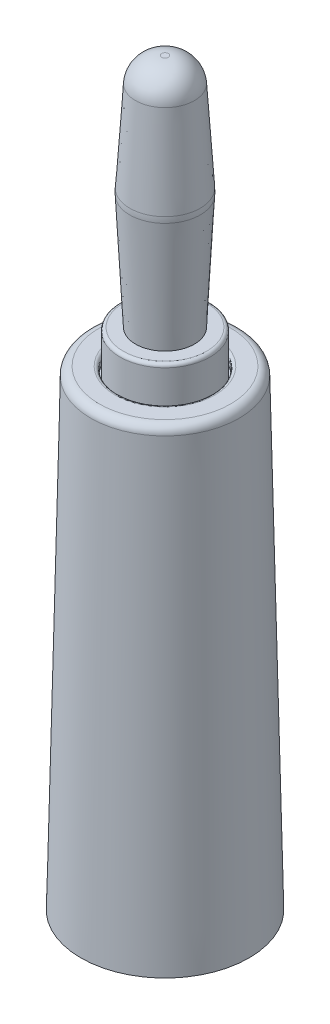
SolidWorks part; units mm, degrees
other "Plastic Cover"
other "Metal Body"
other "Tip"
material "Plain Carbon Steel"
ref_plane "Front Plane" through (0, 0, 0) normal (0, 0, 1) x (1, 0, 0)
ref_plane "Top Plane" through (0, 0, 0) normal (0, 1, 0) x (1, 0, 0)
ref_plane "Right Plane" through (0, 0, 0) normal (1, 0, 0) x (0, 0, -1)
sketch "Sketch1" plane through (0, 0, 0) normal (0, 0, 1) x (1, 0, 0)
  line L0 (0, 0) -> (0, 18)
  line L1 (0, 0) -> (3.45, 0)
  line L2 (3.45, 0) -> (3.45, 13)
  line L3 (3.45, 13) -> (2.68, 13.77)
  line L4 (2.68, 13.77) -> (2.68, 18)
  line L5 (2.68, 18) -> (0, 18)
  dimension "D1" = 2.68
  dimension "D2" = 3.45
  dimension "D3" = 13
  dimension "D4" = 18
  dimension "D5" = 135
revolve "Revolve1" add sketch "Sketch1" angle 360 about L0
sketch "Sketch2" plane through (0, 0, 0) normal (0, -1, 0) x (1, 0, 0)
  circle A0 centre (0, 0) radius 2.55
  dimension "D1" = 5.1
extrude "Cut-Extrude1" cut sketch "Sketch2" against normal blind 11
sketch "Sketch3" plane through (0, 0, 0) normal (0, 0, 1) x (1, 0, 0)
  line L0 (0, 0) -> (0, 18) construction
  line L1 (2.68, 18) -> (-2.68, 18) construction
  line L2 (0, 18) -> (0, 32)
  line L3 (0, 18) -> (1.75, 18)
  line L4 (0, 32) -> (0.2, 32)
  line L5 (1.75, 32) -> (1.75, 30.546) construction
  line L6 (0.2, 32) -> (1.75, 32) construction
  line L7 (0, 25) -> (2.1, 25) construction
  line L8 (1.75, 30.546) -> (2.0939, 25.1717)
  line L9 (2.0962, 24.8282) -> (1.75, 18)
  arc A0 (0.2, 32) -> (1.75, 30.546) centre (0.2, 30.4468) cw
  arc A1 (2.0939, 25.1717) -> (2.0962, 24.8282) centre (-0.8999, 24.9801) cw
  dimension "D6" = 3
  dimension "D1" = 14
  dimension "D2" = 1.75
  dimension "D3" = 1.75
  dimension "D4" = 7
  dimension "D5" = 0.2
  dimension "D7" = 2.1
revolve "Revolve2" add sketch "Sketch3" angle 360 about L2
shell "Shell7" thickness 0.1
sketch "Sketch4" plane through (0, 0, 0) normal (0, 0, 1) x (1, 0, 0)
  line L0 (0, 0) -> (0, 3) construction
  circle A0 centre (0, 3) radius 1.2
  dimension "D1" = 2.4
  dimension "D2" = 3
extrude "Cut-Extrude2" cut sketch "Sketch4" along normal through all
sketch "Sketch5" plane through (0, 0, 0) normal (0, 0, 1) x (1, 0, 0)
  line L0 (0, 0) -> (0, 8) construction
  circle A0 centre (0, 8) radius 1.2
  dimension "D1" = 2.4
  dimension "D2" = 8
extrude "Cut-Extrude3" cut sketch "Sketch5" against normal through all
fillet "Fillet1" radius 0.2 3 edges at (0, 18, -2.68) (0, 13.77, -2.68) (0, 13, -3.45)
sketch "Sketch6" plane through (0, 0, 0) normal (0, 0, 1) x (1, 0, 0)
  line L0 (0, 15.5) -> (0, -12) construction
  line L1 (0, 15.5) -> (0, 18) construction
  line L3 (-1.75, 18) -> (1.75, 18) construction
  line L4 (0, 15.5) -> (2.68, 15.5) construction
  line L5 (0, -12) -> (4, -12) construction
  line L6 (4, -12) -> (5, -12)
  line L7 (2.68, 13.8528) -> (2.68, 17.8) construction
  line L8 (2.68, 15.5) -> (2.68, 14)
  line L9 (2.68, 14) -> (3.68, 13)
  line L10 (3.68, 13) -> (4, -12)
  line L11 (2.68, 15.5) -> (2.78, 15.5)
  line L12 (2.78, 15.5) -> (2.78, 16)
  line L13 (2.78, 16) -> (4.4, 16)
  line L14 (4.4, 16) -> (5, -12)
  dimension "D1" = 2.5
  dimension "D2" = 27.5
  dimension "D3" = 5
  dimension "D4" = 1
  dimension "D5" = 1.5
  dimension "D6" = 225
  dimension "D7" = 2.5
  dimension "D8" = 0.1
  dimension "D9" = 2
  dimension "D10" = 4.4
revolve "Revolve3" add sketch "Sketch6" angle 360 about L0
fillet "Fillet2" radius 0.2 1 edges at (-2.78, 16, 0)
fillet "Fillet3" radius 0.5 1 edges at (-4.4, 16, 0)
